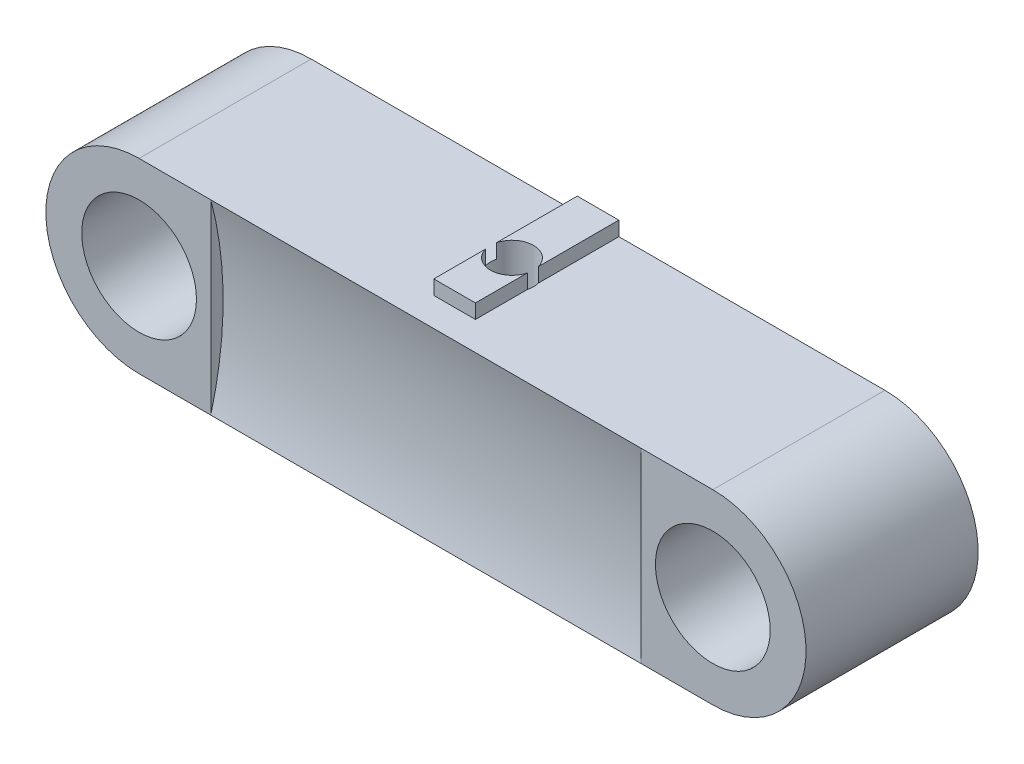
SolidWorks part; units mm, degrees
ref_plane "Front Plane" through (0, 0, 0) normal (0, 0, 1) x (1, 0, 0)
ref_plane "Top Plane" through (0, 0, 0) normal (0, 1, 0) x (1, 0, 0)
ref_plane "Right Plane" through (0, 0, 0) normal (1, 0, 0) x (0, 0, -1)
sketch "Sketch1" plane through (0, 0, 0) normal (0, 0, 1) x (1, 0, 0)
  line L0 (-20, 0) -> (20, 0) construction
  line L1 (-20, 6.5) -> (20, 6.5)
  line L2 (-20, -6.5) -> (20, -6.5)
  arc A0 (-20, 6.5) -> (-20, -6.5) centre (-20, 0) ccw
  arc A1 (20, -6.5) -> (20, 6.5) centre (20, 0) ccw
  circle A2 centre (-20, 0) radius 4
  circle A3 centre (20, 0) radius 4
  point P3 (0, 0)
  point P12 (20, 0)
  dimension "D2" = 6.5
  dimension "D3" = 8
  dimension "D1" = 20
extrude "Main" add sketch "Sketch1" along normal mid plane 12
sketch "Sketch2" plane through (0, 0, 0) normal (1, 0, 0) x (0, 0, -1)
  line L0 (-6, 6.5) -> (-6, -6.5) construction
  line L1 (6.6, 0) -> (-6.6, 0) construction
  line L2 (-6, 6.5) -> (6, 6.5) construction
  line L3 (-6, 6.5) -> (-6, -6.5)
  arc A0 (-6, -6.5) -> (-6, 6.5) centre (-30.1402, 0) ccw
  dimension "D1" = 25
extrude "ScrewBallDriver" cut sketch "Sketch2" against normal mid plane 30
sketch "Sketch3" plane through (0, 0, 0) normal (0, 1, 0) x (1, 0, 0)
  line L1 (-1.45, 6) -> (1.45, 6)
  line L2 (-1.45, 6) -> (-1.45, -4)
  line L3 (-1.45, -4) -> (1.45, -4)
  line L4 (1.45, 6) -> (1.45, -4)
  line L7 (20, 6) -> (-20, 6) construction
  line L8 (-15, -6) -> (15, -6) construction
  point P4 (0, 0)
  point P6 (1.45, -2.2935)
  point P8 (0, 0)
  point P12 (0, -4)
  dimension "D1" = 2.9
  dimension "D2" = 2
extrude "MakerBeamRail" add sketch "Sketch3" along normal blind 7.5
sketch "Sketch4" plane through (0, 7.5, 0) normal (0, 1, 0) x (1, 0, 0)
  circle A0 centre (0, 0) radius 1.5
  point P2 (0, 0)
  dimension "D1" = 3
extrude "MakerBeamHole" cut sketch "Sketch4" against normal through all
